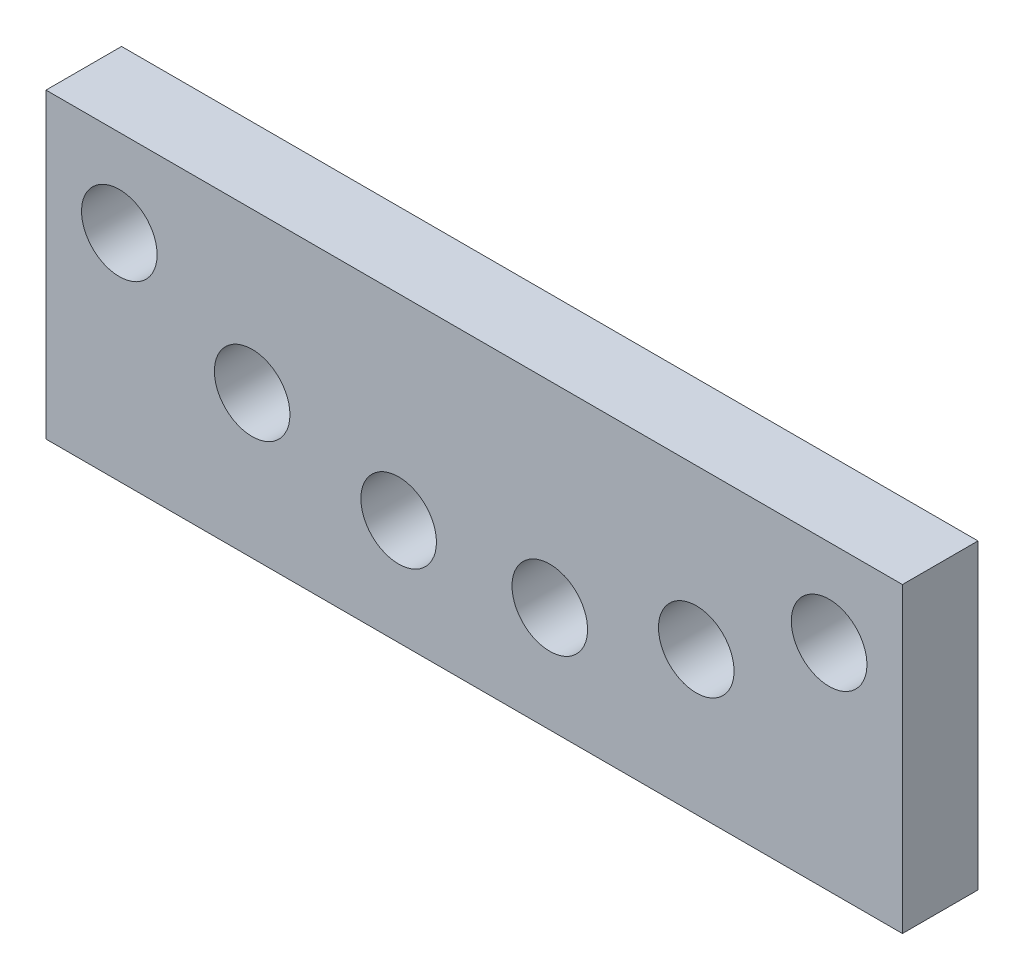
SolidWorks part; units mm, degrees
ref_plane "Plan de face" through (0, 0, 0) normal (0, 0, 1) x (1, 0, 0)
ref_plane "Plan de dessus" through (0, 0, 0) normal (0, 1, 0) x (1, 0, 0)
ref_plane "Plan de droite" through (0, 0, 0) normal (1, 0, 0) x (0, 0, -1)
sketch "Esquisse1" plane through (0, 0, 0) normal (0, 0, 1) x (1, 0, 0)
  line L0 (-85, 0) -> (85, 0)
other "Elément mécano-soudé1"
ref_plane "Plan1" through (-85, 0, 0) normal (1, 0, 0) x (0, 1, 0)
sketch "plat" plane through (-85, 0, 0) normal (1, 0, 0) x (0, 1, 0)
  line L0 (-30, 0) -> (30, 0) construction
  line L1 (-30, 7.5) -> (30, 7.5)
  line L2 (-30, 7.5) -> (-30, -7.5)
  line L3 (-30, -7.5) -> (30, -7.5)
  line L4 (30, 7.5) -> (30, -7.5)
  line L5 (0, 7.5) -> (0, -7.5) construction
  point P8 (0, 0)
  dimension "B" = 60
  dimension "A" = 15
sketch "Esquisse2" plane through (0, 0, 7.5) normal (0, 0, 1) x (1, 0, 0)
  line L0 (0, -9.913) -> (0, 111.087) construction
  line L1 (-70.4463, 12.7085) -> (-44.0779, -1.5991) construction
  line L3 (-25.4932, 30) -> (-46.6864, 143.0303) construction
  line L4 (85, 30) -> (-85, 30) construction
  line L5 (-46.6864, 143.0303) -> (31.9433, 157.7734) construction
  line L6 (31.9433, 157.7734) -> (55.9009, 30) construction
  line L7 (-7.3715, 150.4018) -> (0, 111.087) construction
  line L8 (-44.0779, -1.5991) -> (-15, -8.9797) construction
  line L9 (-15, -8.9797) -> (15, -8.9797) construction
  circle A2 centre (-15, -8.9797) radius 7.5
  circle A3 centre (-44.0779, -1.5991) radius 7.5
  circle A4 centre (-70.4463, 12.7085) radius 7.5
  circle A5 centre (70.4463, 12.7085) radius 7.5
  circle A6 centre (44.0779, -1.5991) radius 7.5
  circle A7 centre (15, -8.9797) radius 7.5
  arc A8 (-70.4463, 12.7085) -> (70.4463, 12.7085) centre (0, 111.087) ccw construction
  point P18 (0, 111.087)
  point P25 (0, 111.087)
  dimension "D1" = 130
  dimension "D3" = 15
  dimension "D2" = 121
  dimension "D5" = 115
  dimension "D6" = 80
  dimension "D8" = 40
  dimension "D4" = 30
extrude "Enlèv. mat.-Extru.1" cut sketch "Esquisse2" against normal through all
